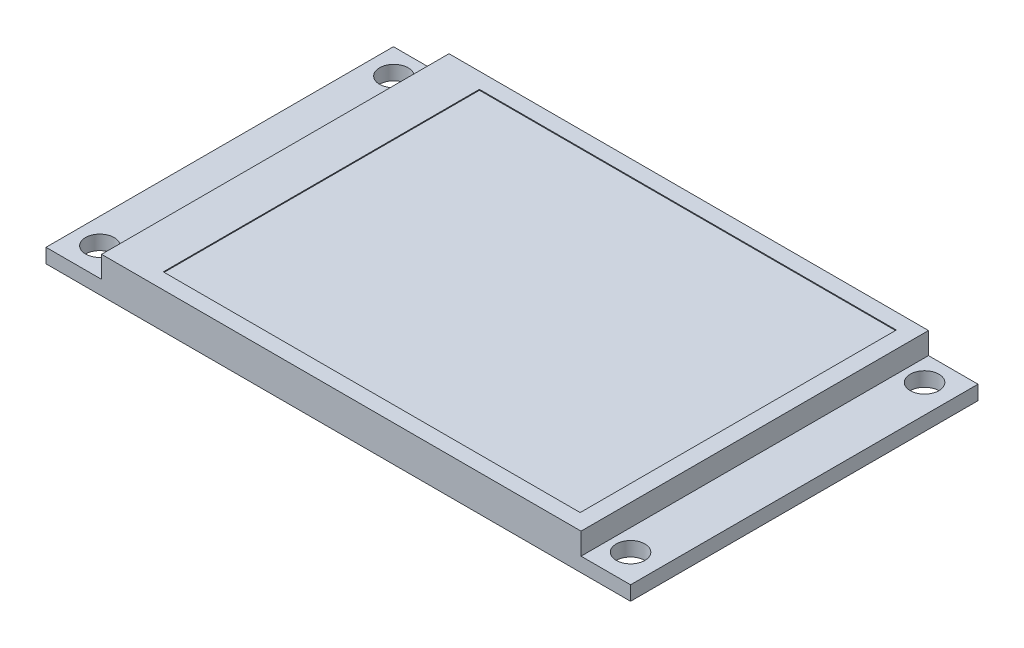
SolidWorks part; units mm, degrees
ref_plane "Front Plane" through (0, 0, 0) normal (0, 0, 1) x (1, 0, 0)
ref_plane "Top Plane" through (0, 0, 0) normal (0, 1, 0) x (1, 0, 0)
ref_plane "Right Plane" through (0, 0, 0) normal (1, 0, 0) x (0, 0, -1)
sketch "Sketch1" plane through (0, 0, 0) normal (0, 1, 0) x (1, 0, 0)
  line L0 (-32.35, 8.0373) -> (-32.35, 18.75) construction
  line L1 (-33.65, -20) -> (33.65, -20)
  line L2 (-33.65, -20) -> (-33.65, 20)
  line L3 (-33.65, 20) -> (33.65, 20)
  line L4 (33.65, -20) -> (33.65, 20)
  line L5 (-33.65, -20) -> (33.65, 20) construction
  line L6 (-33.65, 20) -> (33.65, -20) construction
  line L7 (-30.7, 17.1) -> (30.4, 17.1) construction
  line L8 (-30.7, 17.1) -> (-30.7, -16.75) construction
  line L9 (-30.7, -16.75) -> (30.4, -16.75) construction
  line L10 (30.4, 17.1) -> (30.4, -16.75) construction
  line L11 (-32.35, 18.75) -> (-21.6373, 18.75) construction
  line L12 (32.05, -7.6873) -> (32.05, -18.4) construction
  line L13 (32.05, -18.4) -> (21.3373, -18.4) construction
  circle A0 centre (-30.7, 17.1) radius 1.65
  circle A1 centre (-30.7, -16.75) radius 1.65
  circle A2 centre (30.4, -16.75) radius 1.65
  circle A3 centre (30.4, 17.1) radius 1.65
  point P0 (0, 0)
  dimension "D3" = 3.3
  dimension "D6" = 1.25
  dimension "D1" = 40
  dimension "D2" = 67.3
  dimension "D4" = 1.3
  dimension "D5" = 1.6
  dimension "D7" = 1.6
extrude "Boss-Extrude1" add sketch "Sketch1" along normal blind 1.65
sketch "Sketch2" plane through (0, 1.65, 0) normal (0, 1, 0) x (1, 0, 0)
  line L0 (33.65, 20) -> (-33.65, 20) construction
  line L1 (-27.25, -20) -> (27.95, -20)
  line L2 (-27.25, -20) -> (-27.25, 20)
  line L3 (-27.25, 20) -> (27.95, 20)
  line L4 (27.95, -20) -> (27.95, 20)
  line L5 (-33.65, -20) -> (33.65, -20) construction
  line L6 (-33.65, 20) -> (-33.65, -20) construction
  line L7 (33.65, -20) -> (33.65, 20) construction
  dimension "D1" = 6.4
  dimension "D2" = 5.7
extrude "Boss-Extrude2" add sketch "Sketch2" along normal blind 2.5
sketch "Sketch3" plane through (0, 4.15, 0) normal (0, 1, 0) x (1, 0, 0)
  line L0 (-33.65, 20) -> (-33.65, -20) construction
  line L1 (-21.95, 18.2) -> (26.05, 18.2)
  line L2 (-21.95, 18.2) -> (-21.95, -18.2)
  line L3 (-21.95, -18.2) -> (26.05, -18.2)
  line L4 (26.05, 18.2) -> (26.05, -18.2)
  line L5 (27.95, 20) -> (-27.25, 20) construction
  line L6 (-27.25, -20) -> (27.95, -20) construction
  line L7 (33.65, -20) -> (33.65, 20) construction
  point P10 (33.65, 0)
  dimension "D1" = 11.7
  dimension "D2" = 1.8
  dimension "D3" = 1.8
  dimension "D4" = 7.6
extrude "Cut-Extrude1" cut sketch "Sketch3" against normal blind 0.1
